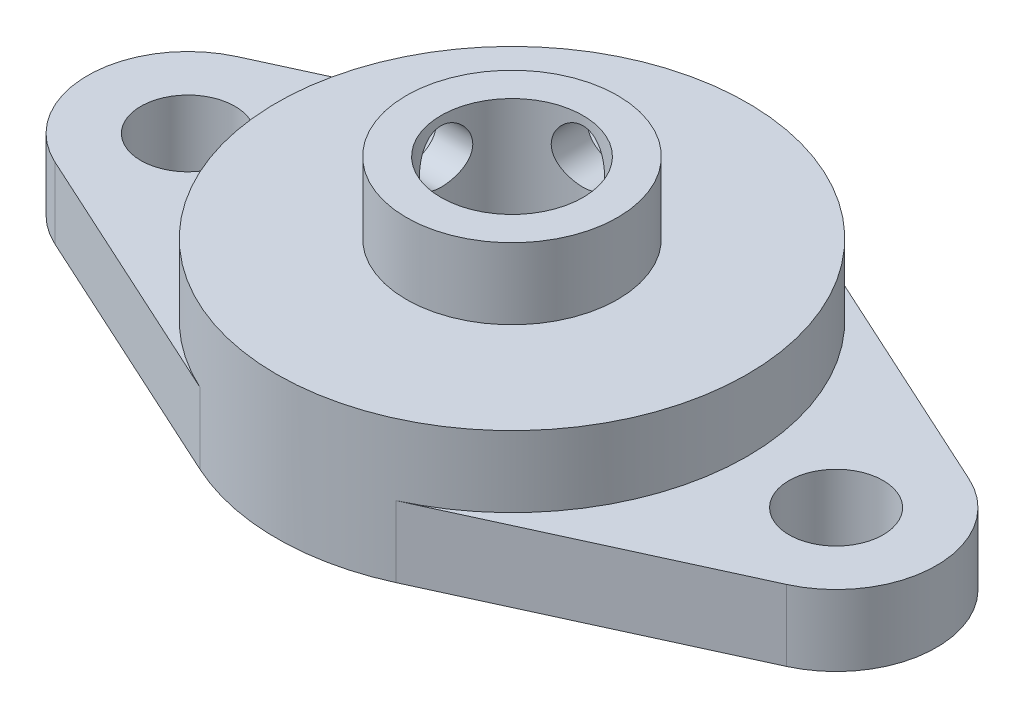
SolidWorks part; units mm, degrees
material "304不锈钢"
ref_plane "前视基准面" through (0, 0, 0) normal (0, 0, 1) x (1, 0, 0)
ref_plane "上视基准面" through (0, 0, 0) normal (0, 1, 0) x (1, 0, 0)
ref_plane "右视基准面" through (0, 0, 0) normal (1, 0, 0) x (0, 0, -1)
sketch "草图1" plane through (0, 0, 0) normal (0, 1, 0) x (1, 0, 0)
  circle A0 centre (0, 0) radius 13.25
  circle A1 centre (0, 0) radius 4
  dimension "D1" = 26.5
  dimension "D2" = 8
extrude "凸台" add sketch "草图1" along normal blind 8
sketch "草图2" plane through (0, 0, 0) normal (0, 1, 0) x (1, 0, 0)
  line L0 (-1000, 0) -> (49000, 0) construction
  line L1 (0, -1000) -> (0, 49000) construction
  line L2 (-20.6029, -5.1368) -> (-5.5178, -12.0464)
  line L3 (-20.6029, 5.1368) -> (-5.5178, 12.0464)
  line L4 (-5.5178, 12.0464) -> (-5.5178, -12.0464)
  line L5 (20.6029, 5.1368) -> (5.5178, 12.0464)
  line L6 (20.6029, -5.1368) -> (5.5178, -12.0464)
  line L7 (5.5178, 12.0464) -> (5.5178, -12.0464)
  circle A0 centre (0, 0) radius 13.25 construction
  circle A1 centre (0, 0) radius 13.25 construction
  circle A2 centre (-18.25, 0) radius 2.65
  circle A3 centre (18.25, 0) radius 2.65
  circle A4 centre (-18.25, 0) radius 5.65 construction
  circle A5 centre (0, 0) radius 13.25 construction
  arc A6 (-20.6029, 5.1368) -> (-20.6029, -5.1368) centre (-18.25, 0) ccw
  arc A7 (20.6029, 5.1368) -> (20.6029, -5.1368) centre (18.25, 0) cw
  dimension "D1" = 5.3
  dimension "D2" = 36.5
  dimension "D3" = 11.3
extrude "固定" add sketch "草图2" along normal blind 4
sketch "草图3" plane through (0, 8, 0) normal (0, 1, 0) x (1, 0, 0)
  circle A0 centre (0, 0) radius 4 construction
  circle A1 centre (0, 0) radius 4
  circle A2 centre (0, 0) radius 5.95
  dimension "D1" = 11.9
extrude "内圈" add sketch "草图3" along normal blind 4
sketch "草图4" plane through (0, 0, 0) normal (0, 0, 1) x (1, 0, 0)
  line L0 (0, -1000) -> (0, 49000) construction
  line L1 (-5.5178, 0) -> (5.5178, 0) construction
  line L2 (4, 12) -> (-4, 12) construction
  circle A0 centre (0, 10) radius 1.5
  point P5 (0, 0)
  dimension "D1" = 3
  dimension "D2" = 2
extrude "紧定" cut sketch "草图4" against normal through all
sketch "草图5" plane through (0, 0, 0) normal (1, 0, 0) x (0, 0, -1)
  line L0 (5.95, 12) -> (-5.95, 12) construction
  line L1 (0, -1000) -> (0, 49000) construction
  circle A0 centre (0, 10) radius 1.5
  dimension "D1" = 3
  dimension "D2" = 2
extrude "紧定2" cut sketch "草图5" against normal through all
